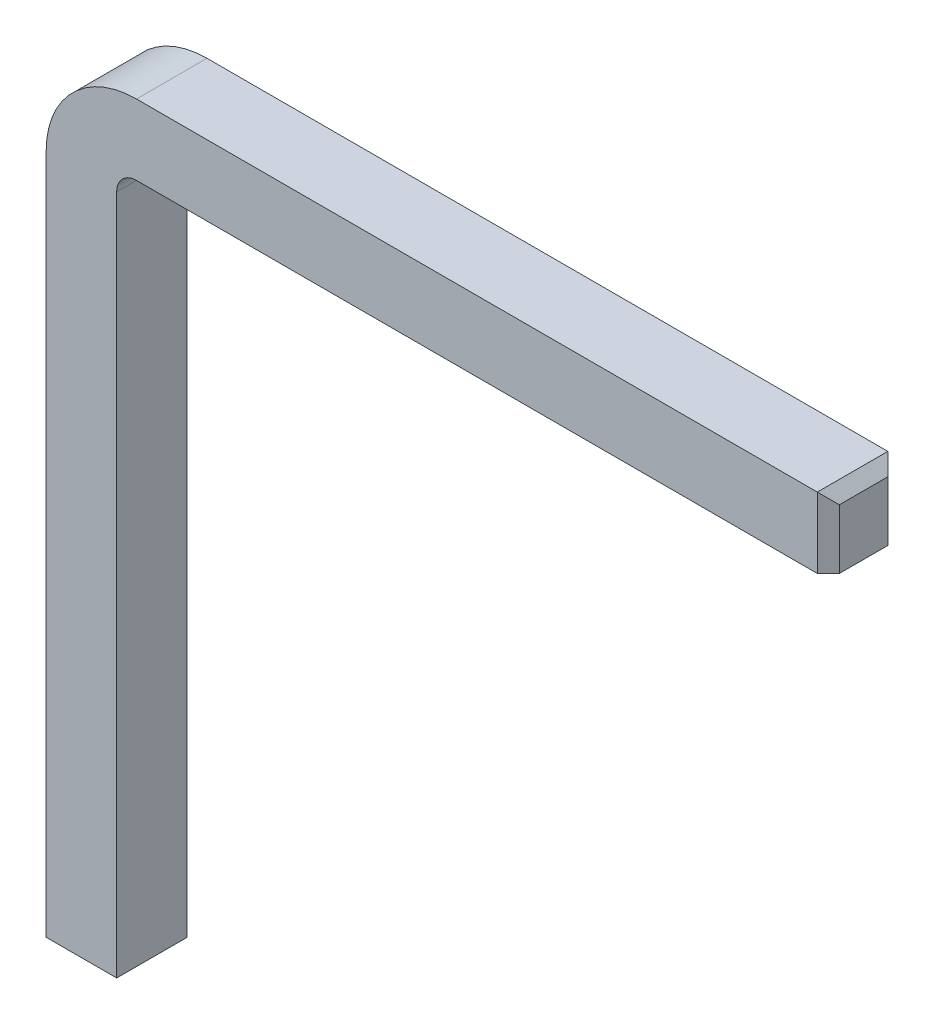
SolidWorks part; units mm, degrees
ref_plane "Front" through (0, 0, 0) normal (0, 0, 1) x (1, 0, 0)
ref_plane "Top" through (0, 0, 0) normal (0, 1, 0) x (1, 0, 0)
ref_plane "Right" through (0, 0, 0) normal (1, 0, 0) x (0, 0, -1)
sketch "Эскиз1" plane through (0, 0, 0) normal (0, 1, 0) x (1, 0, 0)
  line L1 (-0.32, 0.32) -> (0.32, 0.32)
  line L2 (-0.32, 0.32) -> (-0.32, -0.32)
  line L3 (-0.32, -0.32) -> (0.32, -0.32)
  line L4 (0.32, 0.32) -> (0.32, -0.32)
  line L5 (-0.32, 0.32) -> (0.32, -0.32) construction
  line L6 (-0.32, -0.32) -> (0.32, 0.32) construction
  point P0 (0, 0)
  dimension "D1" = 0.64
  dimension "D2" = 0.64
sketch "Эскиз2" plane through (0, 0, 0) normal (0, 0, 1) x (1, 0, 0)
  line L0 (0, 0) -> (0, 6.28)
  line L1 (0.5, 6.78) -> (6.78, 6.78)
  arc A0 (0, 6.28) -> (0.5, 6.78) centre (0.5, 6.28) cw
  point P6 (0, 6.78)
  dimension "D3" = 0.5
  dimension "D1" = 6.78
  dimension "D2" = 6.78
sweep "По траектории1" add profiles "Эскиз1" path "Эскиз2"
chamfer "Фаска1" distance 0.1 angle 45 7 edges at (0, 0, 0.32) (0, 0, -0.32) (-0.32, 0, 0) (0.32, 0, 0) (6.78, 6.78, -0.32) (6.78, 6.78, 0.32) (6.78, 7.1, 0)
equation "\"D2@Эскиз1\"=\"D1@Эскиз1\""
